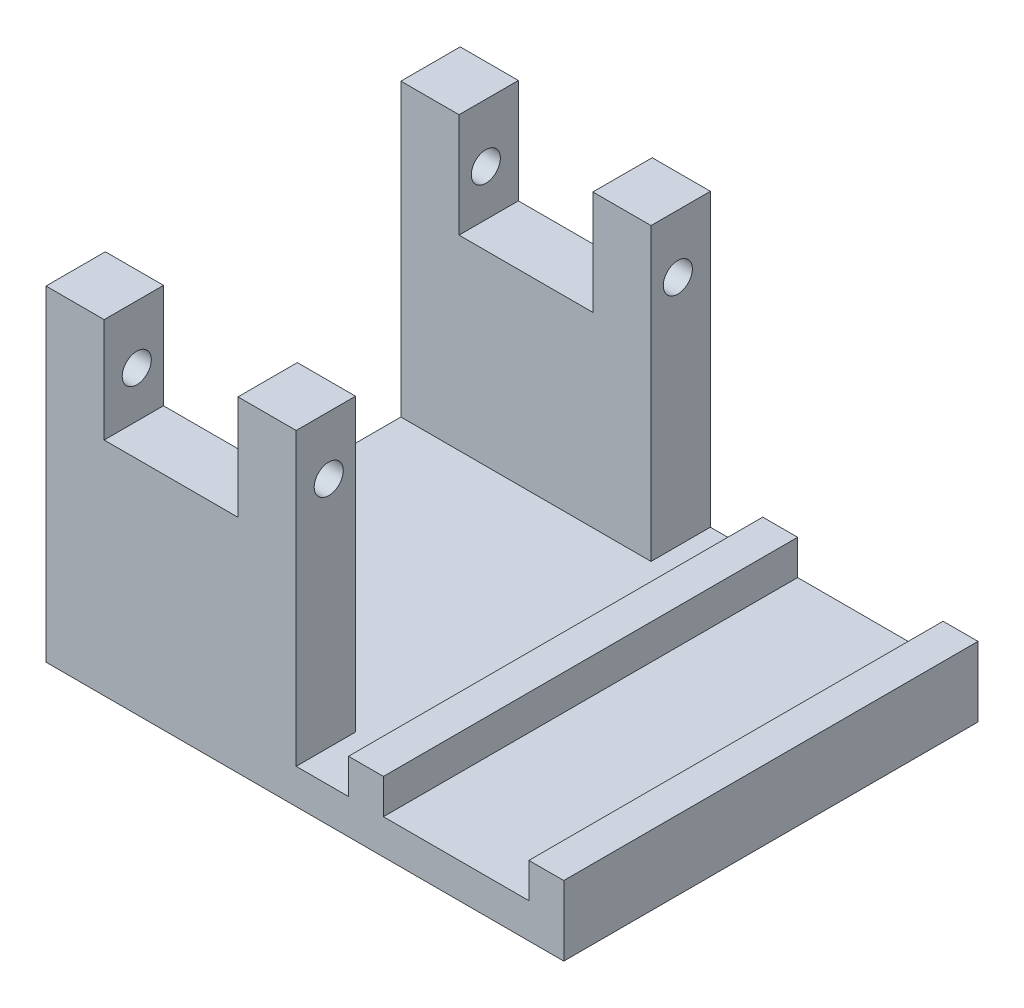
SolidWorks part; units mm, degrees
ref_plane "Front Plane" through (0, 0, 0) normal (0, 0, 1) x (1, 0, 0)
ref_plane "Top Plane" through (0, 0, 0) normal (0, 1, 0) x (1, 0, 0)
ref_plane "Right Plane" through (0, 0, 0) normal (1, 0, 0) x (0, 0, -1)
sketch "Sketch1" plane through (0, 0, 0) normal (0, 1, 0) x (1, 0, 0)
  line L1 (-18.25, -17.8) -> (18.25, -17.8)
  line L2 (-18.25, -17.8) -> (-18.25, 17.8)
  line L3 (-18.25, 17.8) -> (18.25, 17.8)
  line L4 (18.25, -17.8) -> (18.25, 17.8)
  line L5 (-18.25, -17.8) -> (18.25, 17.8) construction
  line L6 (-18.25, 17.8) -> (18.25, -17.8) construction
  point P0 (0, 0)
  dimension "D1" = 36.5
  dimension "D2" = 35.6
extrude "Boss-Extrude1" add sketch "Sketch1" along normal blind 3
sketch "Sketch2" plane through (0, 3, 0) normal (0, 1, 0) x (1, 0, 0)
  line L1 (-18.25, 17.8) -> (-15.25, 17.8)
  line L2 (-18.25, 17.8) -> (-18.25, 12.7)
  line L3 (-18.25, 12.7) -> (-15.25, 12.7)
  line L4 (-15.25, 17.8) -> (-15.25, 12.7)
  line L5 (-18.25, -17.8) -> (-15.25, -17.8)
  line L6 (-18.25, -17.8) -> (-18.25, -12.7)
  line L7 (-18.25, -12.7) -> (-15.25, -12.7)
  line L8 (-15.25, -17.8) -> (-15.25, -12.7)
  line L9 (18.25, 17.8) -> (15.25, 17.8)
  line L10 (18.25, 17.8) -> (18.25, 12.7)
  line L11 (18.25, 12.7) -> (15.25, 12.7)
  line L12 (15.25, 17.8) -> (15.25, 12.7)
  line L13 (18.25, -17.8) -> (15.25, -17.8)
  line L14 (18.25, -17.8) -> (18.25, -12.7)
  line L15 (18.25, -12.7) -> (15.25, -12.7)
  line L16 (15.25, -17.8) -> (15.25, -12.7)
  dimension "D1" = 3
  dimension "D2" = 3
  dimension "D3" = 3
  dimension "D4" = 3
  dimension "D5" = 5.1
  dimension "D6" = 5.1
  dimension "D7" = 5.1
  dimension "D8" = 5.1
extrude "Boss-Extrude2" add sketch "Sketch2" along normal blind 23
sketch "Sketch3" plane through (18.25, 0, 0) normal (1, 0, 0) x (0, 0, -1)
  line L0 (-17.8, 26) -> (-12.7, 26) construction
  line L1 (12.7, 26) -> (17.8, 26) construction
  line L2 (-12.7, 26) -> (-12.7, 3) construction
  line L3 (12.7, 26) -> (12.7, 3) construction
  circle A0 centre (-15, 23) radius 1.35
  circle A1 centre (15, 23) radius 1.35
  dimension "D1" = 2.7
  dimension "D2" = 2.7
  dimension "D3" = 3
  dimension "D4" = 3
  dimension "D5" = 2.3
  dimension "D6" = 2.3
extrude "Cut-Extrude1" cut sketch "Sketch3" against normal through all
sketch "Sketch4" plane through (18.25, 0, 0) normal (1, 0, 0) x (0, 0, -1)
  line L0 (17.8, 26) -> (17.8, 0) construction
  line L1 (-17.8, 0) -> (17.8, 0)
  line L2 (-17.8, 0) -> (-17.8, 3)
  line L3 (-17.8, 3) -> (17.8, 3)
  line L4 (17.8, 0) -> (17.8, 3)
  dimension "D1" = 35.6
  dimension "D2" = 3
extrude "Boss-Extrude3" add sketch "Sketch4" along normal blind 12.5
mirror "Mirror1" about plane through (0, 0, 0) normal (1, 0, 0) of "Boss-Extrude3"
sketch "Sketch5" plane through (0, 0, 0) normal (0, -1, 0) x (1, 0, 0)
  line L1 (30.75, 17.8) -> (33.75, 17.8)
  line L2 (30.75, 17.8) -> (30.75, -17.8)
  line L3 (30.75, -17.8) -> (33.75, -17.8)
  line L4 (33.75, 17.8) -> (33.75, -17.8)
  dimension "D1" = 3
  dimension "D2" = 35.6
extrude "Boss-Extrude4" add sketch "Sketch5" against normal blind 6
mirror "Mirror2" about plane through (0, 0, 0) normal (1, 0, 0) of "Boss-Extrude4"
sketch "Sketch9" plane through (0, 3, 0) normal (0, 1, 0) x (1, 0, 0)
  line L0 (15.25, 17.8) -> (-15.25, 17.8) construction
  line L1 (-10.75, 17.8) -> (10.75, 17.8)
  line L2 (-10.75, 17.8) -> (-10.75, 12.7)
  line L3 (-10.75, 12.7) -> (10.75, 12.7)
  line L4 (10.75, 17.8) -> (10.75, 12.7)
  line L5 (15.25, 17.8) -> (15.25, 12.7) construction
  line L6 (-14.3, 0) -> (14.3, 0) construction
  line L7 (-10.75, -17.8) -> (10.75, -17.8)
  line L8 (10.75, -17.8) -> (10.75, -12.7)
  line L9 (-10.75, -12.7) -> (10.75, -12.7)
  line L10 (-10.75, -17.8) -> (-10.75, -12.7)
  dimension "D1" = 21.5
  dimension "D2" = 4.5
  dimension "D3" = 5.1
extrude "Boss-Extrude6" add sketch "Sketch9" along normal blind 25
sketch "Sketch10" plane through (10.75, 0, 0) normal (1, 0, 0) x (0, 0, -1)
  line L0 (0, 15.4) -> (0, -15.4) construction
  circle A0 centre (15, 23) radius 1.25
  circle A1 centre (-15, 23) radius 1.25
  dimension "D1" = 2.5
  dimension "D2" = 30
extrude "Cut-Extrude4" cut sketch "Sketch10" against normal through all
sketch "Sketch11" plane through (0, 0, -17.8) normal (0, 0, -1) x (-1, 0, 0)
  line L0 (0, 15.4) -> (0, -15.4) construction
  line L1 (-18.25, 26) -> (-15.25, 26)
  line L2 (-18.25, 26) -> (-18.25, 3)
  line L3 (-18.25, 3) -> (-15.25, 3)
  line L4 (-15.25, 26) -> (-15.25, 3)
  line L5 (18.25, 3) -> (15.25, 3)
  line L6 (15.25, 26) -> (15.25, 3)
  line L7 (18.25, 26) -> (15.25, 26)
  line L8 (18.25, 26) -> (18.25, 3)
extrude "Cut-Extrude5" cut sketch "Sketch11" against normal through all
sketch "Sketch12" plane through (0, 0, -17.8) normal (0, 0, -1) x (-1, 0, 0)
  line L0 (-10.75, 28) -> (10.75, 28) construction
  line L1 (-5.75, 28) -> (5.75, 28)
  line L2 (-5.75, 28) -> (-5.75, 19.0369)
  line L3 (-5.75, 19.0369) -> (5.75, 19.0369)
  line L4 (5.75, 28) -> (5.75, 19.0369)
  line L6 (-10.75, 28) -> (-10.75, 3) construction
  line L7 (10.75, 28) -> (10.75, 3) construction
  dimension "D1" = 5
  dimension "D2" = 5
extrude "Cut-Extrude6" cut sketch "Sketch12" against normal through all
sketch "Sketch13" plane through (0, 3, 0) normal (0, 1, 0) x (1, 0, 0)
  line L0 (30.75, 17.8) -> (10.75, 17.8) construction
  line L1 (18.25, 17.8) -> (15.25, 17.8)
  line L2 (18.25, 17.8) -> (18.25, -17.8)
  line L3 (18.25, -17.8) -> (15.25, -17.8)
  line L4 (15.25, 17.8) -> (15.25, -17.8)
  line L5 (30.75, -17.8) -> (10.75, -17.8) construction
  line L6 (30.75, 17.8) -> (30.75, -17.8) construction
  dimension "D1" = 3
  dimension "D2" = 12.5
extrude "Boss-Extrude7" add sketch "Sketch13" along normal up to surface (3 mm away) up to face at (32.25, 6, 0)
sketch "Sketch15" plane through (0, 6, 0) normal (0, 1, 0) x (1, 0, 0)
  line L1 (-33.75, 17.8) -> (-10.75, 17.8)
  line L2 (-33.75, 17.8) -> (-33.75, -17.8)
  line L3 (-33.75, -17.8) -> (-10.75, -17.8)
  line L4 (-10.75, 17.8) -> (-10.75, -17.8)
extrude "Cut-Extrude9" cut sketch "Sketch15" against normal up to surface (6 mm away) up to face at (0, 0, 0)
